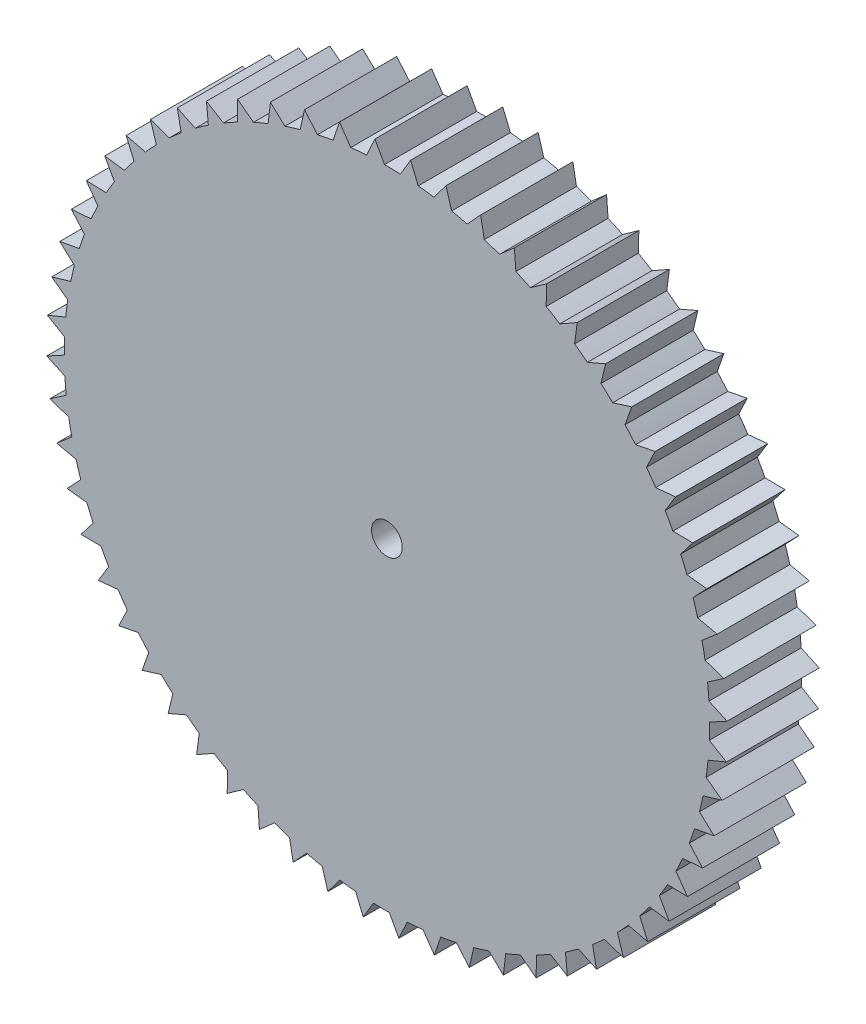
SolidWorks part; units mm, degrees
ref_plane "Front Plane" through (0, 0, 0) normal (0, 0, 1) x (1, 0, 0)
ref_plane "Top Plane" through (0, 0, 0) normal (0, 1, 0) x (1, 0, 0)
ref_plane "Right Plane" through (0, 0, 0) normal (1, 0, 0) x (0, 0, -1)
sketch "Sketch2" plane through (0, 0, 0) normal (0, 1, 0) x (1, 0, 0)
  line L1 (0, 19.1406) -> (0, 42.1406)
  line L2 (21.9625, 25.9706) -> (-21.9625, 25.9706)
  circle A0 centre (0, 19.1406) radius 23
  point P1 (0, 25.9706)
  point P7 (0, 25.9706)
  dimension "D1" = 16.17
  dimension "D2" = 46
ref_plane "Plane1" through (0, 0, -25.9706) normal (0, 0, -1) x (-1, 0, 0)
sketch "Sketch3" plane through (0, 0, -25.9706) normal (0, 0, -1) x (-1, 0, 0)
  line L0 (21.9625, 0) -> (-21.9625, 0)
  line L1 (21.9625, 0) -> (21.9625, 85)
  line L2 (-21.9625, 0) -> (-21.9625, 85)
  line L3 (21.9625, 85) -> (-21.9625, 85)
  line L4 (21.9625, 0) -> (-21.9625, 85) construction
  line L5 (-21.9625, 0) -> (21.9625, 85) construction
  line L9 (34.4493, 57.3155) -> (18.9158, 10.4622)
  line L10 (32.1526, 56.3278) -> (13.3127, 12.5933)
  line L11 (-26.4622, 69.0707) -> (-24.6744, 67.3228)
  line L12 (0, 0) -> (0, 85)
  arc A0 (-24.6744, 67.3228) -> (32.1526, 56.3278) centre (0, 42.5) cw
  arc A1 (23.9765, 17.0024) -> (8.6581, 8.5878) centre (0, 42.5) cw
  arc A2 (-26.4622, 69.0707) -> (34.4493, 57.3155) centre (0, 42.5) cw
  circle A3 centre (16.0681, 11.4063) radius 2
  arc A4 (13.3127, 12.5933) -> (18.9158, 10.4622) centre (16.0681, 11.4063) ccw
  circle A5 centre (0, 42.5) radius 33.5
  circle A6 centre (0, 65.2) radius 10.5
  point P6 (0, 42.5)
  point P10 (16.0681, 11.4063)
  point P13 (-21.9625, 69.7516)
  point P23 (0, 42.5)
  point P26 (0, 76)
  point P27 (0, 75.7)
  point P28 (0.2542, 75.6969)
  point P29 (-1.4579, 75.5983)
  point P31 (0, 72.5)
  dimension "D2" = 5.8944
  dimension "D4" = 0.3
  dimension "D5" = 67
  dimension "D6" = 21
  dimension "D1" = 85
  dimension "D3" = 15.2484
  dimension "D7" = 7.3
extrude "Boss-Extrude1" add sketch "Sketch3" along normal blind 3
sketch "Sketch7" plane through (0, 0, -28.9706) normal (0, 0, -1) x (-1, 0, 0)
  circle A0 centre (0, 65.2) radius 2
extrude "Boss-Extrude4" add sketch "Sketch7" along normal blind 3
sketch "Sketch8" plane through (0, 0, -31.9706) normal (0, 0, -1) x (-1, 0, 0)
  line L0 (0.4, 63.4) -> (-0.4, 63.4)
  line L2 (-0.4, 63.4) -> (0, 62.6)
  line L3 (0, 0) -> (0, 85) construction
  line L4 (0, 62.6) -> (0.4, 63.4)
  point P3 (0, 63.4)
  dimension "D1" = 1.8
  dimension "D2" = 0.8
  dimension "D3" = 0.8
extrude "Boss-Extrude5" add sketch "Sketch8" against normal blind 3
pattern_circular "CirPattern2" count 20 over 360 about axis through (0, 65.1682, 0) along (0, 0, 1) of "Boss-Extrude5"
sketch "Sketch9" plane through (0, 0, -31.9706) normal (0, 0, -1) x (-1, 0, 0)
  circle A0 centre (0, 65.2) radius 0.5
extrude "Cut-Extrude1" cut sketch "Sketch9" against normal blind 6
sketch "Sketch10" plane through (0, 0, -25.9706) normal (0, 0, 1) x (1, 0, 0)
  line L0 (0, 75.7) -> (1.4579, 75.5983)
  line L1 (0.7289, 75.6491) -> (0, 65.2)
  line L2 (0.315, 75.4803) -> (1.115, 75.418)
  line L3 (1.115, 75.418) -> (0.7708, 76.2491)
  line L4 (0.7708, 76.2491) -> (0.315, 75.4803)
  line L5 (0.7708, 76.2491) -> (0.7289, 75.6491)
  point P10 (0.715, 75.4491)
  circle M5 centre (0, 65.2) radius 10.5
  dimension "D1" = 0.8
  dimension "D2" = 0.8
  dimension "D3" = 0.2
extrude "Boss-Extrude6" add sketch "Sketch10" against normal blind 3 contours L5 L4 M5 | L3 L5 M5
pattern_circular "CirPattern3" count 60 over 360 about axis through (0, 65.2, 0) along (0, 0, 1) of "Boss-Extrude6"
